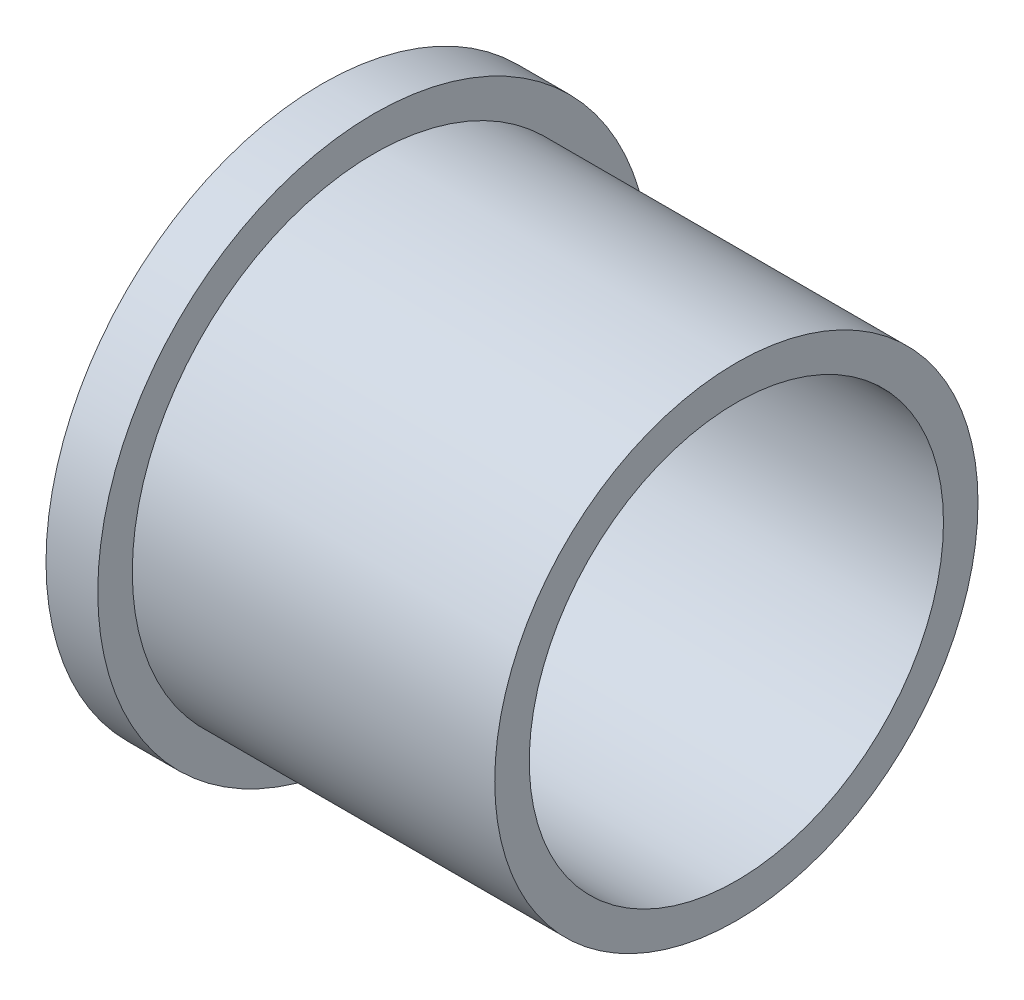
SolidWorks part; units mm, degrees
material "Tin Bearing Bronze"
ref_plane "Front Plane" through (0, 0, 0) normal (0, 0, 1) x (1, 0, 0)
ref_plane "Top Plane" through (0, 0, 0) normal (0, 1, 0) x (1, 0, 0)
ref_plane "Right Plane" through (0, 0, 0) normal (1, 0, 0) x (0, 0, -1)
sketch "Sketch1" plane through (0, 0, 0) normal (1, 0, 0) x (0, 0, -1)
  circle A0 centre (0, 0) radius 19.05
  circle A1 centre (0, 0) radius 22.225
extrude "Boss-Extrude1" add sketch "Sketch1" along normal blind 38.1
sketch "Sketch2" plane through (0, 0, 0) normal (-1, 0, 0) x (0, 0, 1)
  circle A0 centre (0, 0) radius 22.225
  circle A1 centre (0, 0) radius 25.4
extrude "Boss-Extrude2" add sketch "Sketch2" against normal blind 4.7625
